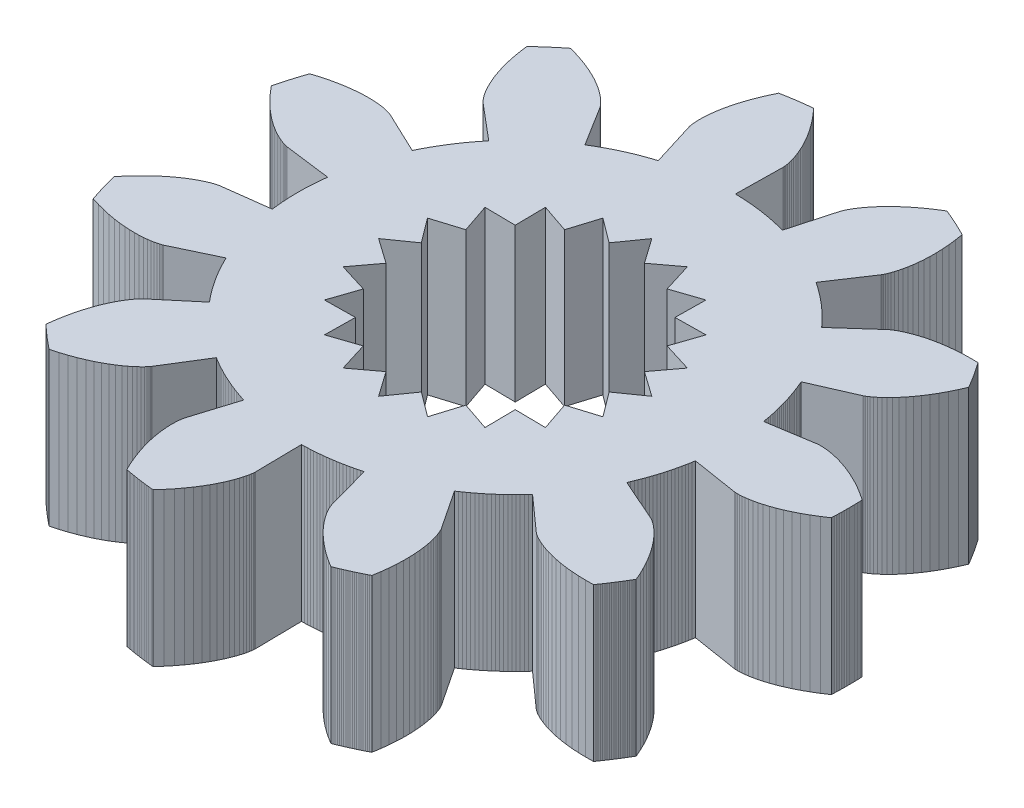
SolidWorks part; units mm, degrees
ref_plane "Front Plane" through (0, 0, 0) normal (0, 0, 1) x (1, 0, 0)
ref_plane "Top Plane" through (0, 0, 0) normal (0, 1, 0) x (1, 0, 0)
ref_plane "Right Plane" through (0, 0, 0) normal (1, 0, 0) x (0, 0, -1)
sketch "Sketch2" plane through (0, 0, 0) normal (0, 1, 0) x (1, 0, 0)
  line L0 (4.1973, -0.6675) -> (5.1042, -0.8117)
  line L1 (5.1042, -0.8117) -> (5.1083, -0.8122)
  line L2 (5.1083, -0.8122) -> (5.1207, -0.8134)
  line L3 (5.1207, -0.8134) -> (5.1415, -0.8146)
  line L4 (5.1415, -0.8146) -> (5.1707, -0.8151)
  line L5 (5.1707, -0.8151) -> (5.2081, -0.8142)
  line L6 (5.2081, -0.8142) -> (5.2538, -0.8113)
  line L7 (5.2538, -0.8113) -> (5.3077, -0.8057)
  line L8 (5.3077, -0.8057) -> (5.3695, -0.7967)
  line L9 (5.3695, -0.7967) -> (5.4391, -0.7838)
  line L10 (5.4391, -0.7838) -> (5.5162, -0.7662)
  line L11 (5.5162, -0.7662) -> (5.6006, -0.7434)
  line L12 (5.6006, -0.7434) -> (5.692, -0.7147)
  line L13 (5.692, -0.7147) -> (5.79, -0.6795)
  line L14 (5.79, -0.6795) -> (5.8942, -0.6374)
  line L15 (5.8942, -0.6374) -> (6.0042, -0.5876)
  line L16 (6.0042, -0.5876) -> (6.1196, -0.5298)
  line L17 (6.1196, -0.5298) -> (6.2399, -0.4633)
  line L18 (6.2399, -0.4633) -> (6.3645, -0.3878)
  line L19 (6.3645, -0.3878) -> (6.4929, -0.3027)
  line L20 (6.4929, -0.3027) -> (6.4944, -0.2708)
  line L21 (6.4944, -0.2708) -> (6.4956, -0.239)
  line L22 (6.4956, -0.239) -> (6.4967, -0.2071)
  line L23 (6.4967, -0.2071) -> (6.4976, -0.1753)
  line L24 (6.4976, -0.1753) -> (6.4984, -0.1434)
  line L25 (6.4984, -0.1434) -> (6.499, -0.1115)
  line L26 (6.499, -0.1115) -> (6.4995, -0.0797)
  line L27 (6.4995, -0.0797) -> (6.4998, -0.0478)
  line L28 (6.4998, -0.0478) -> (6.5, -0.0159)
  line L29 (6.5, -0.0159) -> (6.5, 0.0159)
  line L30 (6.5, 0.0159) -> (6.4998, 0.0478)
  line L31 (6.4998, 0.0478) -> (6.4995, 0.0797)
  line L32 (6.4995, 0.0797) -> (6.499, 0.1115)
  line L33 (6.499, 0.1115) -> (6.4984, 0.1434)
  line L34 (6.4984, 0.1434) -> (6.4976, 0.1753)
  line L35 (6.4976, 0.1753) -> (6.4967, 0.2071)
  line L36 (6.4967, 0.2071) -> (6.4956, 0.239)
  line L37 (6.4956, 0.239) -> (6.4944, 0.2708)
  line L38 (6.4944, 0.2708) -> (6.4929, 0.3027)
  line L39 (6.4929, 0.3027) -> (6.3645, 0.3878)
  line L40 (6.3645, 0.3878) -> (6.2399, 0.4633)
  line L41 (6.2399, 0.4633) -> (6.1196, 0.5298)
  line L42 (6.1196, 0.5298) -> (6.0042, 0.5876)
  line L43 (6.0042, 0.5876) -> (5.8942, 0.6374)
  line L44 (5.8942, 0.6374) -> (5.79, 0.6795)
  line L45 (5.79, 0.6795) -> (5.692, 0.7147)
  line L46 (5.692, 0.7147) -> (5.6006, 0.7434)
  line L47 (5.6006, 0.7434) -> (5.5162, 0.7662)
  line L48 (5.5162, 0.7662) -> (5.4391, 0.7838)
  line L49 (5.4391, 0.7838) -> (5.3695, 0.7967)
  line L50 (5.3695, 0.7967) -> (5.3077, 0.8057)
  line L51 (5.3077, 0.8057) -> (5.2538, 0.8113)
  line L52 (5.2538, 0.8113) -> (5.2081, 0.8142)
  line L53 (5.2081, 0.8142) -> (5.1707, 0.8151)
  line L54 (5.1707, 0.8151) -> (5.1415, 0.8146)
  line L55 (5.1415, 0.8146) -> (5.1207, 0.8134)
  line L56 (5.1207, 0.8134) -> (5.1083, 0.8122)
  line L57 (5.1083, 0.8122) -> (5.1042, 0.8117)
  line L58 (5.1042, 0.8117) -> (4.1973, 0.6675)
  line L59 (4.1973, 0.6675) -> (4.1879, 0.7239)
  line L60 (4.1879, 0.7239) -> (4.1778, 0.7802)
  line L61 (4.1778, 0.7802) -> (4.1669, 0.8364)
  line L62 (4.1669, 0.8364) -> (4.1552, 0.8924)
  line L63 (4.1552, 0.8924) -> (4.1429, 0.9483)
  line L64 (4.1429, 0.9483) -> (4.1297, 1.004)
  line L65 (4.1297, 1.004) -> (4.1158, 1.0595)
  line L66 (4.1158, 1.0595) -> (4.1012, 1.1148)
  line L67 (4.1012, 1.1148) -> (4.0858, 1.1699)
  line L68 (4.0858, 1.1699) -> (4.0697, 1.2248)
  line L69 (4.0697, 1.2248) -> (4.0528, 1.2795)
  line L70 (4.0528, 1.2795) -> (4.0352, 1.3339)
  line L71 (4.0352, 1.3339) -> (4.0169, 1.3881)
  line L72 (4.0169, 1.3881) -> (3.9979, 1.4421)
  line L73 (3.9979, 1.4421) -> (3.9781, 1.4957)
  line L74 (3.9781, 1.4957) -> (3.9576, 1.5492)
  line L75 (3.9576, 1.5492) -> (3.9364, 1.6023)
  line L76 (3.9364, 1.6023) -> (3.9145, 1.6552)
  line L77 (3.9145, 1.6552) -> (3.8918, 1.7077)
  line L78 (3.8918, 1.7077) -> (4.7327, 2.0767)
  line L79 (4.7327, 2.0767) -> (4.7365, 2.0785)
  line L80 (4.7365, 2.0785) -> (4.7476, 2.0842)
  line L81 (4.7476, 2.0842) -> (4.7657, 2.0944)
  line L82 (4.7657, 2.0944) -> (4.7905, 2.1098)
  line L83 (4.7905, 2.1098) -> (4.8215, 2.1308)
  line L84 (4.8215, 2.1308) -> (4.8584, 2.158)
  line L85 (4.8584, 2.158) -> (4.9007, 2.1918)
  line L86 (4.9007, 2.1918) -> (4.9478, 2.2327)
  line L87 (4.9478, 2.2327) -> (4.9994, 2.2813)
  line L88 (4.9994, 2.2813) -> (5.0548, 2.3377)
  line L89 (5.0548, 2.3377) -> (5.1134, 2.4026)
  line L90 (5.1134, 2.4026) -> (5.1748, 2.4761)
  line L91 (5.1748, 2.4761) -> (5.2382, 2.5586)
  line L92 (5.2382, 2.5586) -> (5.3031, 2.6505)
  line L93 (5.3031, 2.6505) -> (5.3688, 2.7518)
  line L94 (5.3688, 2.7518) -> (5.4346, 2.8628)
  line L95 (5.4346, 2.8628) -> (5.4998, 2.9838)
  line L96 (5.4998, 2.9838) -> (5.5638, 3.1147)
  line L97 (5.5638, 3.1147) -> (5.6259, 3.2557)
  line L98 (5.6259, 3.2557) -> (5.6098, 3.2833)
  line L99 (5.6098, 3.2833) -> (5.5937, 3.3107)
  line L100 (5.5937, 3.3107) -> (5.5774, 3.3381)
  line L101 (5.5774, 3.3381) -> (5.5609, 3.3654)
  line L102 (5.5609, 3.3654) -> (5.5444, 3.3927)
  line L103 (5.5444, 3.3927) -> (5.5276, 3.4198)
  line L104 (5.5276, 3.4198) -> (5.5108, 3.4469)
  line L105 (5.5108, 3.4469) -> (5.4938, 3.4739)
  line L106 (5.4938, 3.4739) -> (5.4767, 3.5007)
  line L107 (5.4767, 3.5007) -> (5.4595, 3.5276)
  line L108 (5.4595, 3.5276) -> (5.4422, 3.5543)
  line L109 (5.4422, 3.5543) -> (5.4247, 3.5809)
  line L110 (5.4247, 3.5809) -> (5.407, 3.6075)
  line L111 (5.407, 3.6075) -> (5.3893, 3.634)
  line L112 (5.3893, 3.634) -> (5.3714, 3.6603)
  line L113 (5.3714, 3.6603) -> (5.3534, 3.6866)
  line L114 (5.3534, 3.6866) -> (5.3352, 3.7128)
  line L115 (5.3352, 3.7128) -> (5.317, 3.739)
  line L116 (5.317, 3.739) -> (5.2986, 3.765)
  line L117 (5.2986, 3.765) -> (5.1445, 3.7671)
  line L118 (5.1445, 3.7671) -> (4.9988, 3.7633)
  line L119 (4.9988, 3.7633) -> (4.8617, 3.7542)
  line L120 (4.8617, 3.7542) -> (4.7334, 3.7405)
  line L121 (4.7334, 3.7405) -> (4.6139, 3.7228)
  line L122 (4.6139, 3.7228) -> (4.5035, 3.702)
  line L123 (4.5035, 3.702) -> (4.402, 3.6785)
  line L124 (4.402, 3.6785) -> (4.3097, 3.6533)
  line L125 (4.3097, 3.6533) -> (4.2263, 3.6268)
  line L126 (4.2263, 3.6268) -> (4.1519, 3.5999)
  line L127 (4.1519, 3.5999) -> (4.0864, 3.5732)
  line L128 (4.0864, 3.5732) -> (4.0295, 3.5473)
  line L129 (4.0295, 3.5473) -> (3.9812, 3.5229)
  line L130 (3.9812, 3.5229) -> (3.9412, 3.5007)
  line L131 (3.9412, 3.5007) -> (3.9092, 3.4811)
  line L132 (3.9092, 3.4811) -> (3.8849, 3.465)
  line L133 (3.8849, 3.465) -> (3.8681, 3.4528)
  line L134 (3.8681, 3.4528) -> (3.8583, 3.445)
  line L135 (3.8583, 3.445) -> (3.8551, 3.4424)
  line L136 (3.8551, 3.4424) -> (3.1701, 2.8307)
  line L137 (3.1701, 2.8307) -> (3.1317, 2.8731)
  line L138 (3.1317, 2.8731) -> (3.0927, 2.915)
  line L139 (3.0927, 2.915) -> (3.0532, 2.9564)
  line L140 (3.0532, 2.9564) -> (3.0131, 2.9972)
  line L141 (3.0131, 2.9972) -> (2.9725, 3.0375)
  line L142 (2.9725, 3.0375) -> (2.9314, 3.0773)
  line L143 (2.9314, 3.0773) -> (2.8897, 3.1165)
  line L144 (2.8897, 3.1165) -> (2.8474, 3.1551)
  line L145 (2.8474, 3.1551) -> (2.8047, 3.1931)
  line L146 (2.8047, 3.1931) -> (2.7615, 3.2306)
  line L147 (2.7615, 3.2306) -> (2.7177, 3.2675)
  line L148 (2.7177, 3.2675) -> (2.6735, 3.3038)
  line L149 (2.6735, 3.3038) -> (2.6288, 3.3395)
  line L150 (2.6288, 3.3395) -> (2.5836, 3.3745)
  line L151 (2.5836, 3.3745) -> (2.5379, 3.409)
  line L152 (2.5379, 3.409) -> (2.4918, 3.4429)
  line L153 (2.4918, 3.4429) -> (2.4452, 3.4761)
  line L154 (2.4452, 3.4761) -> (2.3982, 3.5087)
  line L155 (2.3982, 3.5087) -> (2.3508, 3.5407)
  line L156 (2.3508, 3.5407) -> (2.8587, 4.3057)
  line L157 (2.8587, 4.3057) -> (2.8609, 4.3093)
  line L158 (2.8609, 4.3093) -> (2.8671, 4.3201)
  line L159 (2.8671, 4.3201) -> (2.8768, 4.3385)
  line L160 (2.8768, 4.3385) -> (2.8894, 4.3648)
  line L161 (2.8894, 4.3648) -> (2.9041, 4.3993)
  line L162 (2.9041, 4.3993) -> (2.9205, 4.4421)
  line L163 (2.9205, 4.4421) -> (2.9377, 4.4934)
  line L164 (2.9377, 4.4934) -> (2.9553, 4.5533)
  line L165 (2.9553, 4.5533) -> (2.9724, 4.622)
  line L166 (2.9724, 4.622) -> (2.9885, 4.6994)
  line L167 (2.9885, 4.6994) -> (3.0028, 4.7857)
  line L168 (3.0028, 4.7857) -> (3.0146, 4.8807)
  line L169 (3.0146, 4.8807) -> (3.0234, 4.9845)
  line L170 (3.0234, 4.9845) -> (3.0283, 5.0968)
  line L171 (3.0283, 5.0968) -> (3.0288, 5.2175)
  line L172 (3.0288, 5.2175) -> (3.0241, 5.3465)
  line L173 (3.0241, 5.3465) -> (3.0136, 5.4835)
  line L174 (3.0136, 5.4835) -> (2.9966, 5.6283)
  line L175 (2.9966, 5.6283) -> (2.9726, 5.7805)
  line L176 (2.9726, 5.7805) -> (2.9442, 5.795)
  line L177 (2.9442, 5.795) -> (2.9158, 5.8093)
  line L178 (2.9158, 5.8093) -> (2.8872, 5.8236)
  line L179 (2.8872, 5.8236) -> (2.8586, 5.8376)
  line L180 (2.8586, 5.8376) -> (2.83, 5.8516)
  line L181 (2.83, 5.8516) -> (2.8013, 5.8654)
  line L182 (2.8013, 5.8654) -> (2.7725, 5.8791)
  line L183 (2.7725, 5.8791) -> (2.7436, 5.8926)
  line L184 (2.7436, 5.8926) -> (2.7147, 5.906)
  line L185 (2.7147, 5.906) -> (2.6857, 5.9192)
  line L186 (2.6857, 5.9192) -> (2.6566, 5.9323)
  line L187 (2.6566, 5.9323) -> (2.6275, 5.9453)
  line L188 (2.6275, 5.9453) -> (2.5983, 5.9581)
  line L189 (2.5983, 5.9581) -> (2.5691, 5.9707)
  line L190 (2.5691, 5.9707) -> (2.5398, 5.9833)
  line L191 (2.5398, 5.9833) -> (2.5104, 5.9957)
  line L192 (2.5104, 5.9957) -> (2.481, 6.0079)
  line L193 (2.481, 6.0079) -> (2.4515, 6.02)
  line L194 (2.4515, 6.02) -> (2.4219, 6.0319)
  line L195 (2.4219, 6.0319) -> (2.2912, 5.9504)
  line L196 (2.2912, 5.9504) -> (2.1707, 5.8685)
  line L197 (2.1707, 5.8685) -> (2.0603, 5.7867)
  line L198 (2.0603, 5.7867) -> (1.9597, 5.7057)
  line L199 (1.9597, 5.7057) -> (1.8688, 5.6263)
  line L200 (1.8688, 5.6263) -> (1.7871, 5.549)
  line L201 (1.7871, 5.549) -> (1.7145, 5.4745)
  line L202 (1.7145, 5.4745) -> (1.6504, 5.4033)
  line L203 (1.6504, 5.4033) -> (1.5946, 5.336)
  line L204 (1.5946, 5.336) -> (1.5465, 5.2731)
  line L205 (1.5465, 5.2731) -> (1.5059, 5.2152)
  line L206 (1.5059, 5.2152) -> (1.472, 5.1627)
  line L207 (1.472, 5.1627) -> (1.4446, 5.1161)
  line L208 (1.4446, 5.1161) -> (1.4229, 5.0757)
  line L209 (1.4229, 5.0757) -> (1.4066, 5.042)
  line L210 (1.4066, 5.042) -> (1.3949, 5.0153)
  line L211 (1.3949, 5.0153) -> (1.3873, 4.9959)
  line L212 (1.3873, 4.9959) -> (1.3832, 4.9841)
  line L213 (1.3832, 4.9841) -> (1.382, 4.9801)
  line L214 (1.382, 4.9801) -> (1.1365, 4.0952)
  line L215 (1.1365, 4.0952) -> (1.0812, 4.1102)
  line L216 (1.0812, 4.1102) -> (1.0258, 4.1243)
  line L217 (1.0258, 4.1243) -> (0.9702, 4.1378)
  line L218 (0.9702, 4.1378) -> (0.9144, 4.1505)
  line L219 (0.9144, 4.1505) -> (0.8584, 4.1624)
  line L220 (0.8584, 4.1624) -> (0.8023, 4.1736)
  line L221 (0.8023, 4.1736) -> (0.7461, 4.184)
  line L222 (0.7461, 4.184) -> (0.6897, 4.1937)
  line L223 (0.6897, 4.1937) -> (0.6331, 4.2026)
  line L224 (0.6331, 4.2026) -> (0.5765, 4.2107)
  line L225 (0.5765, 4.2107) -> (0.5198, 4.2181)
  line L226 (0.5198, 4.2181) -> (0.4629, 4.2247)
  line L227 (0.4629, 4.2247) -> (0.406, 4.2306)
  line L228 (0.406, 4.2306) -> (0.349, 4.2356)
  line L229 (0.349, 4.2356) -> (0.292, 4.24)
  line L230 (0.292, 4.24) -> (0.2349, 4.2435)
  line L231 (0.2349, 4.2435) -> (0.1777, 4.2463)
  line L232 (0.1777, 4.2463) -> (0.1205, 4.2483)
  line L233 (0.1205, 4.2483) -> (0.0633, 4.2495)
  line L234 (0.0633, 4.2495) -> (0.077, 5.1677)
  line L235 (0.077, 5.1677) -> (0.077, 5.1719)
  line L236 (0.077, 5.1719) -> (0.0764, 5.1844)
  line L237 (0.0764, 5.1844) -> (0.0746, 5.2051)
  line L238 (0.0746, 5.2051) -> (0.0709, 5.234)
  line L239 (0.0709, 5.234) -> (0.0647, 5.271)
  line L240 (0.0647, 5.271) -> (0.0553, 5.3158)
  line L241 (0.0553, 5.3158) -> (0.0421, 5.3683)
  line L242 (0.0421, 5.3683) -> (0.0244, 5.4282)
  line L243 (0.0244, 5.4282) -> (0.0017, 5.4953)
  line L244 (0.0017, 5.4953) -> (-0.0267, 5.5691)
  line L245 (-0.0267, 5.5691) -> (-0.0613, 5.6494)
  line L246 (-0.0613, 5.6494) -> (-0.1027, 5.7358)
  line L247 (-0.1027, 5.7358) -> (-0.1514, 5.8278)
  line L248 (-0.1514, 5.8278) -> (-0.208, 5.9249)
  line L249 (-0.208, 5.9249) -> (-0.2729, 6.0267)
  line L250 (-0.2729, 6.0267) -> (-0.3465, 6.1327)
  line L251 (-0.3465, 6.1327) -> (-0.4294, 6.2423)
  line L252 (-0.4294, 6.2423) -> (-0.522, 6.3549)
  line L253 (-0.522, 6.3549) -> (-0.6245, 6.4699)
  line L254 (-0.6245, 6.4699) -> (-0.6562, 6.4668)
  line L255 (-0.6562, 6.4668) -> (-0.6879, 6.4635)
  line L256 (-0.6879, 6.4635) -> (-0.7196, 6.46)
  line L257 (-0.7196, 6.46) -> (-0.7512, 6.4564)
  line L258 (-0.7512, 6.4564) -> (-0.7829, 6.4527)
  line L259 (-0.7829, 6.4527) -> (-0.8145, 6.4488)
  line L260 (-0.8145, 6.4488) -> (-0.8461, 6.4447)
  line L261 (-0.8461, 6.4447) -> (-0.8777, 6.4405)
  line L262 (-0.8777, 6.4405) -> (-0.9093, 6.4361)
  line L263 (-0.9093, 6.4361) -> (-0.9408, 6.4316)
  line L264 (-0.9408, 6.4316) -> (-0.9723, 6.4269)
  line L265 (-0.9723, 6.4269) -> (-1.0038, 6.422)
  line L266 (-1.0038, 6.422) -> (-1.0353, 6.417)
  line L267 (-1.0353, 6.417) -> (-1.0668, 6.4119)
  line L268 (-1.0668, 6.4119) -> (-1.0982, 6.4066)
  line L269 (-1.0982, 6.4066) -> (-1.1296, 6.4011)
  line L270 (-1.1296, 6.4011) -> (-1.161, 6.3955)
  line L271 (-1.161, 6.3955) -> (-1.1923, 6.3897)
  line L272 (-1.1923, 6.3897) -> (-1.2236, 6.3838)
  line L273 (-1.2236, 6.3838) -> (-1.2896, 6.2445)
  line L274 (-1.2896, 6.2445) -> (-1.3466, 6.1104)
  line L275 (-1.3466, 6.1104) -> (-1.3953, 5.9819)
  line L276 (-1.3953, 5.9819) -> (-1.4361, 5.8595)
  line L277 (-1.4361, 5.8595) -> (-1.4697, 5.7435)
  line L278 (-1.4697, 5.7435) -> (-1.4966, 5.6343)
  line L279 (-1.4966, 5.6343) -> (-1.5175, 5.5324)
  line L280 (-1.5175, 5.5324) -> (-1.5328, 5.4378)
  line L281 (-1.5328, 5.4378) -> (-1.5434, 5.351)
  line L282 (-1.5434, 5.351) -> (-1.5498, 5.2722)
  line L283 (-1.5498, 5.2722) -> (-1.5528, 5.2015)
  line L284 (-1.5528, 5.2015) -> (-1.5528, 5.139)
  line L285 (-1.5528, 5.139) -> (-1.5507, 5.0849)
  line L286 (-1.5507, 5.0849) -> (-1.5471, 5.0393)
  line L287 (-1.5471, 5.0393) -> (-1.5426, 5.002)
  line L288 (-1.5426, 5.002) -> (-1.538, 4.9733)
  line L289 (-1.538, 4.9733) -> (-1.5339, 4.9529)
  line L290 (-1.5339, 4.9529) -> (-1.531, 4.9407)
  line L291 (-1.531, 4.9407) -> (-1.5298, 4.9367)
  line L292 (-1.5298, 4.9367) -> (-1.258, 4.0595)
  line L293 (-1.258, 4.0595) -> (-1.3125, 4.0422)
  line L294 (-1.3125, 4.0422) -> (-1.3668, 4.0242)
  line L295 (-1.3668, 4.0242) -> (-1.4209, 4.0054)
  line L296 (-1.4209, 4.0054) -> (-1.4747, 3.986)
  line L297 (-1.4747, 3.986) -> (-1.5282, 3.9657)
  line L298 (-1.5282, 3.9657) -> (-1.5815, 3.9448)
  line L299 (-1.5815, 3.9448) -> (-1.6344, 3.9232)
  line L300 (-1.6344, 3.9232) -> (-1.6871, 3.9008)
  line L301 (-1.6871, 3.9008) -> (-1.7395, 3.8777)
  line L302 (-1.7395, 3.8777) -> (-1.7915, 3.854)
  line L303 (-1.7915, 3.854) -> (-1.8432, 3.8295)
  line L304 (-1.8432, 3.8295) -> (-1.8946, 3.8043)
  line L305 (-1.8946, 3.8043) -> (-1.9456, 3.7785)
  line L306 (-1.9456, 3.7785) -> (-1.9963, 3.752)
  line L307 (-1.9963, 3.752) -> (-2.0467, 3.7247)
  line L308 (-2.0467, 3.7247) -> (-2.0966, 3.6968)
  line L309 (-2.0966, 3.6968) -> (-2.1462, 3.6683)
  line L310 (-2.1462, 3.6683) -> (-2.1954, 3.6391)
  line L311 (-2.1954, 3.6391) -> (-2.2442, 3.6092)
  line L312 (-2.2442, 3.6092) -> (-2.7291, 4.389)
  line L313 (-2.7291, 4.389) -> (-2.7314, 4.3925)
  line L314 (-2.7314, 4.3925) -> (-2.7386, 4.4027)
  line L315 (-2.7386, 4.4027) -> (-2.7514, 4.4191)
  line L316 (-2.7514, 4.4191) -> (-2.7701, 4.4415)
  line L317 (-2.7701, 4.4415) -> (-2.7953, 4.4692)
  line L318 (-2.7953, 4.4692) -> (-2.8274, 4.5018)
  line L319 (-2.8274, 4.5018) -> (-2.8669, 4.5389)
  line L320 (-2.8669, 4.5389) -> (-2.9142, 4.5797)
  line L321 (-2.9142, 4.5797) -> (-2.9695, 4.6238)
  line L322 (-2.9695, 4.6238) -> (-3.0333, 4.6706)
  line L323 (-3.0333, 4.6706) -> (-3.1058, 4.7195)
  line L324 (-3.1058, 4.7195) -> (-3.1874, 4.7697)
  line L325 (-3.1874, 4.7697) -> (-3.2781, 4.8208)
  line L326 (-3.2781, 4.8208) -> (-3.3782, 4.8719)
  line L327 (-3.3782, 4.8719) -> (-3.4878, 4.9225)
  line L328 (-3.4878, 4.9225) -> (-3.6071, 4.9718)
  line L329 (-3.6071, 4.9718) -> (-3.7361, 5.0192)
  line L330 (-3.7361, 5.0192) -> (-3.8748, 5.0639)
  line L331 (-3.8748, 5.0639) -> (-4.0232, 5.1053)
  line L332 (-4.0232, 5.1053) -> (-4.0482, 5.0855)
  line L333 (-4.0482, 5.0855) -> (-4.0731, 5.0656)
  line L334 (-4.0731, 5.0656) -> (-4.0979, 5.0455)
  line L335 (-4.0979, 5.0455) -> (-4.1226, 5.0254)
  line L336 (-4.1226, 5.0254) -> (-4.1472, 5.0051)
  line L337 (-4.1472, 5.0051) -> (-4.1717, 4.9847)
  line L338 (-4.1717, 4.9847) -> (-4.1961, 4.9642)
  line L339 (-4.1961, 4.9642) -> (-4.2203, 4.9435)
  line L340 (-4.2203, 4.9435) -> (-4.2445, 4.9228)
  line L341 (-4.2445, 4.9228) -> (-4.2686, 4.9019)
  line L342 (-4.2686, 4.9019) -> (-4.2926, 4.8809)
  line L343 (-4.2926, 4.8809) -> (-4.3165, 4.8598)
  line L344 (-4.3165, 4.8598) -> (-4.3403, 4.8386)
  line L345 (-4.3403, 4.8386) -> (-4.3639, 4.8173)
  line L346 (-4.3639, 4.8173) -> (-4.3875, 4.7958)
  line L347 (-4.3875, 4.7958) -> (-4.411, 4.7742)
  line L348 (-4.411, 4.7742) -> (-4.4343, 4.7526)
  line L349 (-4.4343, 4.7526) -> (-4.4576, 4.7308)
  line L350 (-4.4576, 4.7308) -> (-4.4807, 4.7088)
  line L351 (-4.4807, 4.7088) -> (-4.4609, 4.5561)
  line L352 (-4.4609, 4.5561) -> (-4.4364, 4.4124)
  line L353 (-4.4364, 4.4124) -> (-4.4079, 4.278)
  line L354 (-4.4079, 4.278) -> (-4.376, 4.1529)
  line L355 (-4.376, 4.1529) -> (-4.3416, 4.0372)
  line L356 (-4.3416, 4.0372) -> (-4.3052, 3.9308)
  line L357 (-4.3052, 3.9308) -> (-4.2676, 3.8337)
  line L358 (-4.2676, 3.8337) -> (-4.2294, 3.7459)
  line L359 (-4.2294, 3.7459) -> (-4.1914, 3.6671)
  line L360 (-4.1914, 3.6671) -> (-4.1542, 3.5973)
  line L361 (-4.1542, 3.5973) -> (-4.1184, 3.5363)
  line L362 (-4.1184, 3.5363) -> (-4.0847, 3.4837)
  line L363 (-4.0847, 3.4837) -> (-4.0536, 3.4393)
  line L364 (-4.0536, 3.4393) -> (-4.0259, 3.4029)
  line L365 (-4.0259, 3.4029) -> (-4.002, 3.374)
  line L366 (-4.002, 3.374) -> (-3.9826, 3.3523)
  line L367 (-3.9826, 3.3523) -> (-3.9681, 3.3373)
  line L368 (-3.9681, 3.3373) -> (-3.9591, 3.3287)
  line L369 (-3.9591, 3.3287) -> (-3.956, 3.3259)
  line L370 (-3.956, 3.3259) -> (-3.2531, 2.735)
  line L371 (-3.2531, 2.735) -> (-3.2896, 2.6909)
  line L372 (-3.2896, 2.6909) -> (-3.3255, 2.6464)
  line L373 (-3.3255, 2.6464) -> (-3.3608, 2.6014)
  line L374 (-3.3608, 2.6014) -> (-3.3956, 2.5559)
  line L375 (-3.3956, 2.5559) -> (-3.4297, 2.51)
  line L376 (-3.4297, 2.51) -> (-3.4631, 2.4636)
  line L377 (-3.4631, 2.4636) -> (-3.496, 2.4167)
  line L378 (-3.496, 2.4167) -> (-3.5282, 2.3695)
  line L379 (-3.5282, 2.3695) -> (-3.5598, 2.3217)
  line L380 (-3.5598, 2.3217) -> (-3.5907, 2.2736)
  line L381 (-3.5907, 2.2736) -> (-3.621, 2.2251)
  line L382 (-3.621, 2.2251) -> (-3.6506, 2.1761)
  line L383 (-3.6506, 2.1761) -> (-3.6796, 2.1268)
  line L384 (-3.6796, 2.1268) -> (-3.7079, 2.077)
  line L385 (-3.7079, 2.077) -> (-3.7355, 2.0269)
  line L386 (-3.7355, 2.0269) -> (-3.7625, 1.9765)
  line L387 (-3.7625, 1.9765) -> (-3.7887, 1.9256)
  line L388 (-3.7887, 1.9256) -> (-3.8143, 1.8745)
  line L389 (-3.8143, 1.8745) -> (-3.8392, 1.8229)
  line L390 (-3.8392, 1.8229) -> (-4.6687, 2.2168)
  line L391 (-4.6687, 2.2168) -> (-4.6725, 2.2185)
  line L392 (-4.6725, 2.2185) -> (-4.6841, 2.2231)
  line L393 (-4.6841, 2.2231) -> (-4.7038, 2.2301)
  line L394 (-4.7038, 2.2301) -> (-4.7316, 2.2388)
  line L395 (-4.7316, 2.2388) -> (-4.7678, 2.2485)
  line L396 (-4.7678, 2.2485) -> (-4.8125, 2.2586)
  line L397 (-4.8125, 2.2586) -> (-4.8657, 2.2684)
  line L398 (-4.8657, 2.2684) -> (-4.9275, 2.2772)
  line L399 (-4.9275, 2.2772) -> (-4.998, 2.2844)
  line L400 (-4.998, 2.2844) -> (-5.0769, 2.2892)
  line L401 (-5.0769, 2.2892) -> (-5.1643, 2.2911)
  line L402 (-5.1643, 2.2911) -> (-5.2601, 2.2893)
  line L403 (-5.2601, 2.2893) -> (-5.364, 2.2832)
  line L404 (-5.364, 2.2832) -> (-5.4759, 2.2721)
  line L405 (-5.4759, 2.2721) -> (-5.5955, 2.2554)
  line L406 (-5.5955, 2.2554) -> (-5.7225, 2.2324)
  line L407 (-5.7225, 2.2324) -> (-5.8566, 2.2025)
  line L408 (-5.8566, 2.2025) -> (-5.9975, 2.1651)
  line L409 (-5.9975, 2.1651) -> (-6.1447, 2.1197)
  line L410 (-6.1447, 2.1197) -> (-6.155, 2.0895)
  line L411 (-6.155, 2.0895) -> (-6.1652, 2.0593)
  line L412 (-6.1652, 2.0593) -> (-6.1752, 2.0291)
  line L413 (-6.1752, 2.0291) -> (-6.1851, 1.9988)
  line L414 (-6.1851, 1.9988) -> (-6.1948, 1.9684)
  line L415 (-6.1948, 1.9684) -> (-6.2044, 1.938)
  line L416 (-6.2044, 1.938) -> (-6.2138, 1.9076)
  line L417 (-6.2138, 1.9076) -> (-6.2231, 1.8771)
  line L418 (-6.2231, 1.8771) -> (-6.2322, 1.8465)
  line L419 (-6.2322, 1.8465) -> (-6.2412, 1.816)
  line L420 (-6.2412, 1.816) -> (-6.25, 1.7853)
  line L421 (-6.25, 1.7853) -> (-6.2587, 1.7547)
  line L422 (-6.2587, 1.7547) -> (-6.2672, 1.724)
  line L423 (-6.2672, 1.724) -> (-6.2756, 1.6932)
  line L424 (-6.2756, 1.6932) -> (-6.2838, 1.6624)
  line L425 (-6.2838, 1.6624) -> (-6.2919, 1.6316)
  line L426 (-6.2919, 1.6316) -> (-6.2998, 1.6007)
  line L427 (-6.2998, 1.6007) -> (-6.3076, 1.5698)
  line L428 (-6.3076, 1.5698) -> (-6.3152, 1.5389)
  line L429 (-6.3152, 1.5389) -> (-6.216, 1.421)
  line L430 (-6.216, 1.421) -> (-6.1177, 1.3134)
  line L431 (-6.1177, 1.3134) -> (-6.021, 1.2158)
  line L432 (-6.021, 1.2158) -> (-5.9266, 1.1278)
  line L433 (-5.9266, 1.1278) -> (-5.835, 1.049)
  line L434 (-5.835, 1.049) -> (-5.7469, 0.9792)
  line L435 (-5.7469, 0.9792) -> (-5.6628, 0.9179)
  line L436 (-5.6628, 0.9179) -> (-5.5832, 0.8646)
  line L437 (-5.5832, 0.8646) -> (-5.5086, 0.819)
  line L438 (-5.5086, 0.819) -> (-5.4396, 0.7804)
  line L439 (-5.4396, 0.7804) -> (-5.3764, 0.7483)
  line L440 (-5.3764, 0.7483) -> (-5.3197, 0.7223)
  line L441 (-5.3197, 0.7223) -> (-5.2696, 0.7018)
  line L442 (-5.2696, 0.7018) -> (-5.2265, 0.6861)
  line L443 (-5.2265, 0.6861) -> (-5.1908, 0.6747)
  line L444 (-5.1908, 0.6747) -> (-5.1628, 0.6669)
  line L445 (-5.1628, 0.6669) -> (-5.1425, 0.6622)
  line L446 (-5.1425, 0.6622) -> (-5.1302, 0.6598)
  line L447 (-5.1302, 0.6598) -> (-5.1261, 0.6592)
  line L448 (-5.1261, 0.6592) -> (-4.2153, 0.5421)
  line L449 (-4.2153, 0.5421) -> (-4.2222, 0.4853)
  line L450 (-4.2222, 0.4853) -> (-4.2284, 0.4284)
  line L451 (-4.2284, 0.4284) -> (-4.2337, 0.3714)
  line L452 (-4.2337, 0.3714) -> (-4.2384, 0.3144)
  line L453 (-4.2384, 0.3144) -> (-4.2422, 0.2573)
  line L454 (-4.2422, 0.2573) -> (-4.2453, 0.2002)
  line L455 (-4.2453, 0.2002) -> (-4.2476, 0.143)
  line L456 (-4.2476, 0.143) -> (-4.2491, 0.0858)
  line L457 (-4.2491, 0.0858) -> (-4.2499, 0.0286)
  line L458 (-4.2499, 0.0286) -> (-4.2499, -0.0286)
  line L459 (-4.2499, -0.0286) -> (-4.2491, -0.0858)
  line L460 (-4.2491, -0.0858) -> (-4.2476, -0.143)
  line L461 (-4.2476, -0.143) -> (-4.2453, -0.2002)
  line L462 (-4.2453, -0.2002) -> (-4.2422, -0.2573)
  line L463 (-4.2422, -0.2573) -> (-4.2384, -0.3144)
  line L464 (-4.2384, -0.3144) -> (-4.2337, -0.3714)
  line L465 (-4.2337, -0.3714) -> (-4.2284, -0.4284)
  line L466 (-4.2284, -0.4284) -> (-4.2222, -0.4853)
  line L467 (-4.2222, -0.4853) -> (-4.2153, -0.5421)
  line L468 (-4.2153, -0.5421) -> (-5.1261, -0.6592)
  line L469 (-5.1261, -0.6592) -> (-5.1302, -0.6598)
  line L470 (-5.1302, -0.6598) -> (-5.1425, -0.6622)
  line L471 (-5.1425, -0.6622) -> (-5.1628, -0.6669)
  line L472 (-5.1628, -0.6669) -> (-5.1908, -0.6747)
  line L473 (-5.1908, -0.6747) -> (-5.2265, -0.6861)
  line L474 (-5.2265, -0.6861) -> (-5.2696, -0.7018)
  line L475 (-5.2696, -0.7018) -> (-5.3197, -0.7223)
  line L476 (-5.3197, -0.7223) -> (-5.3764, -0.7483)
  line L477 (-5.3764, -0.7483) -> (-5.4396, -0.7804)
  line L478 (-5.4396, -0.7804) -> (-5.5086, -0.819)
  line L479 (-5.5086, -0.819) -> (-5.5832, -0.8646)
  line L480 (-5.5832, -0.8646) -> (-5.6628, -0.9179)
  line L481 (-5.6628, -0.9179) -> (-5.7469, -0.9792)
  line L482 (-5.7469, -0.9792) -> (-5.835, -1.049)
  line L483 (-5.835, -1.049) -> (-5.9266, -1.1278)
  line L484 (-5.9266, -1.1278) -> (-6.021, -1.2158)
  line L485 (-6.021, -1.2158) -> (-6.1177, -1.3134)
  line L486 (-6.1177, -1.3134) -> (-6.216, -1.421)
  line L487 (-6.216, -1.421) -> (-6.3152, -1.5389)
  line L488 (-6.3152, -1.5389) -> (-6.3076, -1.5698)
  line L489 (-6.3076, -1.5698) -> (-6.2998, -1.6007)
  line L490 (-6.2998, -1.6007) -> (-6.2919, -1.6316)
  line L491 (-6.2919, -1.6316) -> (-6.2838, -1.6624)
  line L492 (-6.2838, -1.6624) -> (-6.2756, -1.6932)
  line L493 (-6.2756, -1.6932) -> (-6.2672, -1.724)
  line L494 (-6.2672, -1.724) -> (-6.2587, -1.7547)
  line L495 (-6.2587, -1.7547) -> (-6.25, -1.7853)
  line L496 (-6.25, -1.7853) -> (-6.2412, -1.816)
  line L497 (-6.2412, -1.816) -> (-6.2322, -1.8465)
  line L498 (-6.2322, -1.8465) -> (-6.2231, -1.8771)
  line L499 (-6.2231, -1.8771) -> (-6.2138, -1.9076)
  line L500 (-6.2138, -1.9076) -> (-6.2044, -1.938)
  line L501 (-6.2044, -1.938) -> (-6.1948, -1.9684)
  line L502 (-6.1948, -1.9684) -> (-6.1851, -1.9988)
  line L503 (-6.1851, -1.9988) -> (-6.1752, -2.0291)
  line L504 (-6.1752, -2.0291) -> (-6.1652, -2.0593)
  line L505 (-6.1652, -2.0593) -> (-6.155, -2.0895)
  line L506 (-6.155, -2.0895) -> (-6.1447, -2.1197)
  line L507 (-6.1447, -2.1197) -> (-5.9975, -2.1651)
  line L508 (-5.9975, -2.1651) -> (-5.8566, -2.2025)
  line L509 (-5.8566, -2.2025) -> (-5.7225, -2.2324)
  line L510 (-5.7225, -2.2324) -> (-5.5955, -2.2554)
  line L511 (-5.5955, -2.2554) -> (-5.4759, -2.2721)
  line L512 (-5.4759, -2.2721) -> (-5.364, -2.2832)
  line L513 (-5.364, -2.2832) -> (-5.2601, -2.2893)
  line L514 (-5.2601, -2.2893) -> (-5.1643, -2.2911)
  line L515 (-5.1643, -2.2911) -> (-5.0769, -2.2892)
  line L516 (-5.0769, -2.2892) -> (-4.998, -2.2844)
  line L517 (-4.998, -2.2844) -> (-4.9275, -2.2772)
  line L518 (-4.9275, -2.2772) -> (-4.8657, -2.2684)
  line L519 (-4.8657, -2.2684) -> (-4.8125, -2.2586)
  line L520 (-4.8125, -2.2586) -> (-4.7678, -2.2485)
  line L521 (-4.7678, -2.2485) -> (-4.7316, -2.2388)
  line L522 (-4.7316, -2.2388) -> (-4.7038, -2.2301)
  line L523 (-4.7038, -2.2301) -> (-4.6841, -2.2231)
  line L524 (-4.6841, -2.2231) -> (-4.6725, -2.2185)
  line L525 (-4.6725, -2.2185) -> (-4.6687, -2.2168)
  line L526 (-4.6687, -2.2168) -> (-3.8392, -1.8229)
  line L527 (-3.8392, -1.8229) -> (-3.8143, -1.8745)
  line L528 (-3.8143, -1.8745) -> (-3.7887, -1.9256)
  line L529 (-3.7887, -1.9256) -> (-3.7625, -1.9765)
  line L530 (-3.7625, -1.9765) -> (-3.7355, -2.0269)
  line L531 (-3.7355, -2.0269) -> (-3.7079, -2.077)
  line L532 (-3.7079, -2.077) -> (-3.6796, -2.1268)
  line L533 (-3.6796, -2.1268) -> (-3.6506, -2.1761)
  line L534 (-3.6506, -2.1761) -> (-3.621, -2.2251)
  line L535 (-3.621, -2.2251) -> (-3.5907, -2.2736)
  line L536 (-3.5907, -2.2736) -> (-3.5598, -2.3217)
  line L537 (-3.5598, -2.3217) -> (-3.5282, -2.3695)
  line L538 (-3.5282, -2.3695) -> (-3.496, -2.4167)
  line L539 (-3.496, -2.4167) -> (-3.4631, -2.4636)
  line L540 (-3.4631, -2.4636) -> (-3.4297, -2.51)
  line L541 (-3.4297, -2.51) -> (-3.3956, -2.5559)
  line L542 (-3.3956, -2.5559) -> (-3.3608, -2.6014)
  line L543 (-3.3608, -2.6014) -> (-3.3255, -2.6464)
  line L544 (-3.3255, -2.6464) -> (-3.2896, -2.6909)
  line L545 (-3.2896, -2.6909) -> (-3.2531, -2.735)
  line L546 (-3.2531, -2.735) -> (-3.956, -3.3259)
  line L547 (-3.956, -3.3259) -> (-3.9591, -3.3287)
  line L548 (-3.9591, -3.3287) -> (-3.9681, -3.3373)
  line L549 (-3.9681, -3.3373) -> (-3.9826, -3.3523)
  line L550 (-3.9826, -3.3523) -> (-4.002, -3.374)
  line L551 (-4.002, -3.374) -> (-4.0259, -3.4029)
  line L552 (-4.0259, -3.4029) -> (-4.0536, -3.4393)
  line L553 (-4.0536, -3.4393) -> (-4.0847, -3.4837)
  line L554 (-4.0847, -3.4837) -> (-4.1184, -3.5363)
  line L555 (-4.1184, -3.5363) -> (-4.1542, -3.5973)
  line L556 (-4.1542, -3.5973) -> (-4.1914, -3.6671)
  line L557 (-4.1914, -3.6671) -> (-4.2294, -3.7459)
  line L558 (-4.2294, -3.7459) -> (-4.2676, -3.8337)
  line L559 (-4.2676, -3.8337) -> (-4.3052, -3.9308)
  line L560 (-4.3052, -3.9308) -> (-4.3416, -4.0372)
  line L561 (-4.3416, -4.0372) -> (-4.376, -4.1529)
  line L562 (-4.376, -4.1529) -> (-4.4079, -4.278)
  line L563 (-4.4079, -4.278) -> (-4.4364, -4.4124)
  line L564 (-4.4364, -4.4124) -> (-4.4609, -4.5561)
  line L565 (-4.4609, -4.5561) -> (-4.4807, -4.7088)
  line L566 (-4.4807, -4.7088) -> (-4.4576, -4.7308)
  line L567 (-4.4576, -4.7308) -> (-4.4343, -4.7526)
  line L568 (-4.4343, -4.7526) -> (-4.411, -4.7742)
  line L569 (-4.411, -4.7742) -> (-4.3875, -4.7958)
  line L570 (-4.3875, -4.7958) -> (-4.3639, -4.8173)
  line L571 (-4.3639, -4.8173) -> (-4.3403, -4.8386)
  line L572 (-4.3403, -4.8386) -> (-4.3165, -4.8598)
  line L573 (-4.3165, -4.8598) -> (-4.2926, -4.8809)
  line L574 (-4.2926, -4.8809) -> (-4.2686, -4.9019)
  line L575 (-4.2686, -4.9019) -> (-4.2445, -4.9228)
  line L576 (-4.2445, -4.9228) -> (-4.2203, -4.9435)
  line L577 (-4.2203, -4.9435) -> (-4.1961, -4.9642)
  line L578 (-4.1961, -4.9642) -> (-4.1717, -4.9847)
  line L579 (-4.1717, -4.9847) -> (-4.1472, -5.0051)
  line L580 (-4.1472, -5.0051) -> (-4.1226, -5.0254)
  line L581 (-4.1226, -5.0254) -> (-4.0979, -5.0455)
  line L582 (-4.0979, -5.0455) -> (-4.0731, -5.0656)
  line L583 (-4.0731, -5.0656) -> (-4.0482, -5.0855)
  line L584 (-4.0482, -5.0855) -> (-4.0232, -5.1053)
  line L585 (-4.0232, -5.1053) -> (-3.8748, -5.0639)
  line L586 (-3.8748, -5.0639) -> (-3.7361, -5.0192)
  line L587 (-3.7361, -5.0192) -> (-3.6071, -4.9718)
  line L588 (-3.6071, -4.9718) -> (-3.4878, -4.9225)
  line L589 (-3.4878, -4.9225) -> (-3.3782, -4.8719)
  line L590 (-3.3782, -4.8719) -> (-3.2781, -4.8208)
  line L591 (-3.2781, -4.8208) -> (-3.1874, -4.7697)
  line L592 (-3.1874, -4.7697) -> (-3.1058, -4.7195)
  line L593 (-3.1058, -4.7195) -> (-3.0333, -4.6706)
  line L594 (-3.0333, -4.6706) -> (-2.9695, -4.6238)
  line L595 (-2.9695, -4.6238) -> (-2.9142, -4.5797)
  line L596 (-2.9142, -4.5797) -> (-2.8669, -4.5389)
  line L597 (-2.8669, -4.5389) -> (-2.8274, -4.5018)
  line L598 (-2.8274, -4.5018) -> (-2.7953, -4.4692)
  line L599 (-2.7953, -4.4692) -> (-2.7701, -4.4415)
  line L600 (-2.7701, -4.4415) -> (-2.7514, -4.4191)
  line L601 (-2.7514, -4.4191) -> (-2.7386, -4.4027)
  line L602 (-2.7386, -4.4027) -> (-2.7314, -4.3925)
  line L603 (-2.7314, -4.3925) -> (-2.7291, -4.389)
  line L604 (-2.7291, -4.389) -> (-2.2442, -3.6092)
  line L605 (-2.2442, -3.6092) -> (-2.1954, -3.6391)
  line L606 (-2.1954, -3.6391) -> (-2.1462, -3.6683)
  line L607 (-2.1462, -3.6683) -> (-2.0966, -3.6968)
  line L608 (-2.0966, -3.6968) -> (-2.0467, -3.7247)
  line L609 (-2.0467, -3.7247) -> (-1.9963, -3.752)
  line L610 (-1.9963, -3.752) -> (-1.9456, -3.7785)
  line L611 (-1.9456, -3.7785) -> (-1.8946, -3.8043)
  line L612 (-1.8946, -3.8043) -> (-1.8432, -3.8295)
  line L613 (-1.8432, -3.8295) -> (-1.7915, -3.854)
  line L614 (-1.7915, -3.854) -> (-1.7395, -3.8777)
  line L615 (-1.7395, -3.8777) -> (-1.6871, -3.9008)
  line L616 (-1.6871, -3.9008) -> (-1.6344, -3.9232)
  line L617 (-1.6344, -3.9232) -> (-1.5815, -3.9448)
  line L618 (-1.5815, -3.9448) -> (-1.5282, -3.9657)
  line L619 (-1.5282, -3.9657) -> (-1.4747, -3.986)
  line L620 (-1.4747, -3.986) -> (-1.4209, -4.0054)
  line L621 (-1.4209, -4.0054) -> (-1.3668, -4.0242)
  line L622 (-1.3668, -4.0242) -> (-1.3125, -4.0422)
  line L623 (-1.3125, -4.0422) -> (-1.258, -4.0595)
  line L624 (-1.258, -4.0595) -> (-1.5298, -4.9367)
  line L625 (-1.5298, -4.9367) -> (-1.531, -4.9407)
  line L626 (-1.531, -4.9407) -> (-1.5339, -4.9529)
  line L627 (-1.5339, -4.9529) -> (-1.538, -4.9733)
  line L628 (-1.538, -4.9733) -> (-1.5426, -5.002)
  line L629 (-1.5426, -5.002) -> (-1.5471, -5.0393)
  line L630 (-1.5471, -5.0393) -> (-1.5507, -5.0849)
  line L631 (-1.5507, -5.0849) -> (-1.5528, -5.139)
  line L632 (-1.5528, -5.139) -> (-1.5528, -5.2015)
  line L633 (-1.5528, -5.2015) -> (-1.5498, -5.2722)
  line L634 (-1.5498, -5.2722) -> (-1.5434, -5.351)
  line L635 (-1.5434, -5.351) -> (-1.5328, -5.4378)
  line L636 (-1.5328, -5.4378) -> (-1.5175, -5.5324)
  line L637 (-1.5175, -5.5324) -> (-1.4966, -5.6343)
  line L638 (-1.4966, -5.6343) -> (-1.4697, -5.7435)
  line L639 (-1.4697, -5.7435) -> (-1.4361, -5.8595)
  line L640 (-1.4361, -5.8595) -> (-1.3953, -5.9819)
  line L641 (-1.3953, -5.9819) -> (-1.3466, -6.1104)
  line L642 (-1.3466, -6.1104) -> (-1.2896, -6.2445)
  line L643 (-1.2896, -6.2445) -> (-1.2236, -6.3838)
  line L644 (-1.2236, -6.3838) -> (-1.1923, -6.3897)
  line L645 (-1.1923, -6.3897) -> (-1.161, -6.3955)
  line L646 (-1.161, -6.3955) -> (-1.1296, -6.4011)
  line L647 (-1.1296, -6.4011) -> (-1.0982, -6.4066)
  line L648 (-1.0982, -6.4066) -> (-1.0668, -6.4119)
  line L649 (-1.0668, -6.4119) -> (-1.0353, -6.417)
  line L650 (-1.0353, -6.417) -> (-1.0038, -6.422)
  line L651 (-1.0038, -6.422) -> (-0.9723, -6.4269)
  line L652 (-0.9723, -6.4269) -> (-0.9408, -6.4316)
  line L653 (-0.9408, -6.4316) -> (-0.9093, -6.4361)
  line L654 (-0.9093, -6.4361) -> (-0.8777, -6.4405)
  line L655 (-0.8777, -6.4405) -> (-0.8461, -6.4447)
  line L656 (-0.8461, -6.4447) -> (-0.8145, -6.4488)
  line L657 (-0.8145, -6.4488) -> (-0.7829, -6.4527)
  line L658 (-0.7829, -6.4527) -> (-0.7512, -6.4564)
  line L659 (-0.7512, -6.4564) -> (-0.7196, -6.46)
  line L660 (-0.7196, -6.46) -> (-0.6879, -6.4635)
  line L661 (-0.6879, -6.4635) -> (-0.6562, -6.4668)
  line L662 (-0.6562, -6.4668) -> (-0.6245, -6.4699)
  line L663 (-0.6245, -6.4699) -> (-0.522, -6.3549)
  line L664 (-0.522, -6.3549) -> (-0.4294, -6.2423)
  line L665 (-0.4294, -6.2423) -> (-0.3465, -6.1327)
  line L666 (-0.3465, -6.1327) -> (-0.2729, -6.0267)
  line L667 (-0.2729, -6.0267) -> (-0.208, -5.9249)
  line L668 (-0.208, -5.9249) -> (-0.1514, -5.8278)
  line L669 (-0.1514, -5.8278) -> (-0.1027, -5.7358)
  line L670 (-0.1027, -5.7358) -> (-0.0613, -5.6494)
  line L671 (-0.0613, -5.6494) -> (-0.0267, -5.5691)
  line L672 (-0.0267, -5.5691) -> (0.0017, -5.4953)
  line L673 (0.0017, -5.4953) -> (0.0244, -5.4282)
  line L674 (0.0244, -5.4282) -> (0.0421, -5.3683)
  line L675 (0.0421, -5.3683) -> (0.0553, -5.3158)
  line L676 (0.0553, -5.3158) -> (0.0647, -5.271)
  line L677 (0.0647, -5.271) -> (0.0709, -5.234)
  line L678 (0.0709, -5.234) -> (0.0746, -5.2051)
  line L679 (0.0746, -5.2051) -> (0.0764, -5.1844)
  line L680 (0.0764, -5.1844) -> (0.077, -5.1719)
  line L681 (0.077, -5.1719) -> (0.077, -5.1677)
  line L682 (0.077, -5.1677) -> (0.0633, -4.2495)
  line L683 (0.0633, -4.2495) -> (0.1205, -4.2483)
  line L684 (0.1205, -4.2483) -> (0.1777, -4.2463)
  line L685 (0.1777, -4.2463) -> (0.2349, -4.2435)
  line L686 (0.2349, -4.2435) -> (0.292, -4.24)
  line L687 (0.292, -4.24) -> (0.349, -4.2356)
  line L688 (0.349, -4.2356) -> (0.406, -4.2306)
  line L689 (0.406, -4.2306) -> (0.4629, -4.2247)
  line L690 (0.4629, -4.2247) -> (0.5198, -4.2181)
  line L691 (0.5198, -4.2181) -> (0.5765, -4.2107)
  line L692 (0.5765, -4.2107) -> (0.6331, -4.2026)
  line L693 (0.6331, -4.2026) -> (0.6897, -4.1937)
  line L694 (0.6897, -4.1937) -> (0.7461, -4.184)
  line L695 (0.7461, -4.184) -> (0.8023, -4.1736)
  line L696 (0.8023, -4.1736) -> (0.8584, -4.1624)
  line L697 (0.8584, -4.1624) -> (0.9144, -4.1505)
  line L698 (0.9144, -4.1505) -> (0.9702, -4.1378)
  line L699 (0.9702, -4.1378) -> (1.0258, -4.1243)
  line L700 (1.0258, -4.1243) -> (1.0812, -4.1102)
  line L701 (1.0812, -4.1102) -> (1.1365, -4.0952)
  line L702 (1.1365, -4.0952) -> (1.382, -4.9801)
  line L703 (1.382, -4.9801) -> (1.3832, -4.9841)
  line L704 (1.3832, -4.9841) -> (1.3873, -4.9959)
  line L705 (1.3873, -4.9959) -> (1.3949, -5.0153)
  line L706 (1.3949, -5.0153) -> (1.4066, -5.042)
  line L707 (1.4066, -5.042) -> (1.4229, -5.0757)
  line L708 (1.4229, -5.0757) -> (1.4446, -5.1161)
  line L709 (1.4446, -5.1161) -> (1.472, -5.1627)
  line L710 (1.472, -5.1627) -> (1.5059, -5.2152)
  line L711 (1.5059, -5.2152) -> (1.5465, -5.2731)
  line L712 (1.5465, -5.2731) -> (1.5946, -5.336)
  line L713 (1.5946, -5.336) -> (1.6504, -5.4033)
  line L714 (1.6504, -5.4033) -> (1.7145, -5.4745)
  line L715 (1.7145, -5.4745) -> (1.7871, -5.549)
  line L716 (1.7871, -5.549) -> (1.8688, -5.6263)
  line L717 (1.8688, -5.6263) -> (1.9597, -5.7057)
  line L718 (1.9597, -5.7057) -> (2.0603, -5.7867)
  line L719 (2.0603, -5.7867) -> (2.1707, -5.8685)
  line L720 (2.1707, -5.8685) -> (2.2912, -5.9504)
  line L721 (2.2912, -5.9504) -> (2.4219, -6.0319)
  line L722 (2.4219, -6.0319) -> (2.4515, -6.02)
  line L723 (2.4515, -6.02) -> (2.481, -6.0079)
  line L724 (2.481, -6.0079) -> (2.5104, -5.9957)
  line L725 (2.5104, -5.9957) -> (2.5398, -5.9833)
  line L726 (2.5398, -5.9833) -> (2.5691, -5.9707)
  line L727 (2.5691, -5.9707) -> (2.5983, -5.9581)
  line L728 (2.5983, -5.9581) -> (2.6275, -5.9453)
  line L729 (2.6275, -5.9453) -> (2.6566, -5.9323)
  line L730 (2.6566, -5.9323) -> (2.6857, -5.9192)
  line L731 (2.6857, -5.9192) -> (2.7147, -5.906)
  line L732 (2.7147, -5.906) -> (2.7436, -5.8926)
  line L733 (2.7436, -5.8926) -> (2.7725, -5.8791)
  line L734 (2.7725, -5.8791) -> (2.8013, -5.8654)
  line L735 (2.8013, -5.8654) -> (2.83, -5.8516)
  line L736 (2.83, -5.8516) -> (2.8586, -5.8376)
  line L737 (2.8586, -5.8376) -> (2.8872, -5.8236)
  line L738 (2.8872, -5.8236) -> (2.9158, -5.8093)
  line L739 (2.9158, -5.8093) -> (2.9442, -5.795)
  line L740 (2.9442, -5.795) -> (2.9726, -5.7805)
  line L741 (2.9726, -5.7805) -> (2.9966, -5.6283)
  line L742 (2.9966, -5.6283) -> (3.0136, -5.4835)
  line L743 (3.0136, -5.4835) -> (3.0241, -5.3465)
  line L744 (3.0241, -5.3465) -> (3.0288, -5.2175)
  line L745 (3.0288, -5.2175) -> (3.0283, -5.0968)
  line L746 (3.0283, -5.0968) -> (3.0234, -4.9845)
  line L747 (3.0234, -4.9845) -> (3.0146, -4.8807)
  line L748 (3.0146, -4.8807) -> (3.0028, -4.7857)
  line L749 (3.0028, -4.7857) -> (2.9885, -4.6994)
  line L750 (2.9885, -4.6994) -> (2.9724, -4.622)
  line L751 (2.9724, -4.622) -> (2.9553, -4.5533)
  line L752 (2.9553, -4.5533) -> (2.9377, -4.4934)
  line L753 (2.9377, -4.4934) -> (2.9205, -4.4421)
  line L754 (2.9205, -4.4421) -> (2.9041, -4.3993)
  line L755 (2.9041, -4.3993) -> (2.8894, -4.3648)
  line L756 (2.8894, -4.3648) -> (2.8768, -4.3385)
  line L757 (2.8768, -4.3385) -> (2.8671, -4.3201)
  line L758 (2.8671, -4.3201) -> (2.8609, -4.3093)
  line L759 (2.8609, -4.3093) -> (2.8587, -4.3057)
  line L760 (2.8587, -4.3057) -> (2.3508, -3.5407)
  line L761 (2.3508, -3.5407) -> (2.3982, -3.5087)
  line L762 (2.3982, -3.5087) -> (2.4452, -3.4761)
  line L763 (2.4452, -3.4761) -> (2.4918, -3.4429)
  line L764 (2.4918, -3.4429) -> (2.5379, -3.409)
  line L765 (2.5379, -3.409) -> (2.5836, -3.3745)
  line L766 (2.5836, -3.3745) -> (2.6288, -3.3395)
  line L767 (2.6288, -3.3395) -> (2.6735, -3.3038)
  line L768 (2.6735, -3.3038) -> (2.7177, -3.2675)
  line L769 (2.7177, -3.2675) -> (2.7615, -3.2306)
  line L770 (2.7615, -3.2306) -> (2.8047, -3.1931)
  line L771 (2.8047, -3.1931) -> (2.8474, -3.1551)
  line L772 (2.8474, -3.1551) -> (2.8897, -3.1165)
  line L773 (2.8897, -3.1165) -> (2.9314, -3.0773)
  line L774 (2.9314, -3.0773) -> (2.9725, -3.0375)
  line L775 (2.9725, -3.0375) -> (3.0131, -2.9972)
  line L776 (3.0131, -2.9972) -> (3.0532, -2.9564)
  line L777 (3.0532, -2.9564) -> (3.0927, -2.915)
  line L778 (3.0927, -2.915) -> (3.1317, -2.8731)
  line L779 (3.1317, -2.8731) -> (3.1701, -2.8307)
  line L780 (3.1701, -2.8307) -> (3.8551, -3.4424)
  line L781 (3.8551, -3.4424) -> (3.8583, -3.445)
  line L782 (3.8583, -3.445) -> (3.8681, -3.4528)
  line L783 (3.8681, -3.4528) -> (3.8849, -3.465)
  line L784 (3.8849, -3.465) -> (3.9092, -3.4811)
  line L785 (3.9092, -3.4811) -> (3.9412, -3.5007)
  line L786 (3.9412, -3.5007) -> (3.9812, -3.5229)
  line L787 (3.9812, -3.5229) -> (4.0295, -3.5473)
  line L788 (4.0295, -3.5473) -> (4.0864, -3.5732)
  line L789 (4.0864, -3.5732) -> (4.1519, -3.5999)
  line L790 (4.1519, -3.5999) -> (4.2263, -3.6268)
  line L791 (4.2263, -3.6268) -> (4.3097, -3.6533)
  line L792 (4.3097, -3.6533) -> (4.402, -3.6785)
  line L793 (4.402, -3.6785) -> (4.5035, -3.702)
  line L794 (4.5035, -3.702) -> (4.6139, -3.7228)
  line L795 (4.6139, -3.7228) -> (4.7334, -3.7405)
  line L796 (4.7334, -3.7405) -> (4.8617, -3.7542)
  line L797 (4.8617, -3.7542) -> (4.9988, -3.7633)
  line L798 (4.9988, -3.7633) -> (5.1445, -3.7671)
  line L799 (5.1445, -3.7671) -> (5.2986, -3.765)
  line L800 (5.2986, -3.765) -> (5.317, -3.739)
  line L801 (5.317, -3.739) -> (5.3352, -3.7128)
  line L802 (5.3352, -3.7128) -> (5.3534, -3.6866)
  line L803 (5.3534, -3.6866) -> (5.3714, -3.6603)
  line L804 (5.3714, -3.6603) -> (5.3893, -3.634)
  line L805 (5.3893, -3.634) -> (5.407, -3.6075)
  line L806 (5.407, -3.6075) -> (5.4247, -3.5809)
  line L807 (5.4247, -3.5809) -> (5.4422, -3.5543)
  line L808 (5.4422, -3.5543) -> (5.4595, -3.5276)
  line L809 (5.4595, -3.5276) -> (5.4767, -3.5007)
  line L810 (5.4767, -3.5007) -> (5.4938, -3.4739)
  line L811 (5.4938, -3.4739) -> (5.5108, -3.4469)
  line L812 (5.5108, -3.4469) -> (5.5276, -3.4198)
  line L813 (5.5276, -3.4198) -> (5.5444, -3.3927)
  line L814 (5.5444, -3.3927) -> (5.5609, -3.3654)
  line L815 (5.5609, -3.3654) -> (5.5774, -3.3381)
  line L816 (5.5774, -3.3381) -> (5.5937, -3.3107)
  line L817 (5.5937, -3.3107) -> (5.6098, -3.2833)
  line L818 (5.6098, -3.2833) -> (5.6259, -3.2557)
  line L819 (5.6259, -3.2557) -> (5.5638, -3.1147)
  line L820 (5.5638, -3.1147) -> (5.4998, -2.9838)
  line L821 (5.4998, -2.9838) -> (5.4346, -2.8628)
  line L822 (5.4346, -2.8628) -> (5.3688, -2.7518)
  line L823 (5.3688, -2.7518) -> (5.3031, -2.6505)
  line L824 (5.3031, -2.6505) -> (5.2382, -2.5586)
  line L825 (5.2382, -2.5586) -> (5.1748, -2.4761)
  line L826 (5.1748, -2.4761) -> (5.1134, -2.4026)
  line L827 (5.1134, -2.4026) -> (5.0548, -2.3377)
  line L828 (5.0548, -2.3377) -> (4.9994, -2.2813)
  line L829 (4.9994, -2.2813) -> (4.9478, -2.2327)
  line L830 (4.9478, -2.2327) -> (4.9007, -2.1918)
  line L831 (4.9007, -2.1918) -> (4.8584, -2.158)
  line L832 (4.8584, -2.158) -> (4.8215, -2.1308)
  line L833 (4.8215, -2.1308) -> (4.7905, -2.1098)
  line L834 (4.7905, -2.1098) -> (4.7657, -2.0944)
  line L835 (4.7657, -2.0944) -> (4.7476, -2.0842)
  line L836 (4.7476, -2.0842) -> (4.7365, -2.0785)
  line L837 (4.7365, -2.0785) -> (4.7327, -2.0767)
  line L838 (4.7327, -2.0767) -> (3.8918, -1.7077)
  line L839 (3.8918, -1.7077) -> (3.9145, -1.6552)
  line L840 (3.9145, -1.6552) -> (3.9364, -1.6023)
  line L841 (3.9364, -1.6023) -> (3.9576, -1.5492)
  line L842 (3.9576, -1.5492) -> (3.9781, -1.4957)
  line L843 (3.9781, -1.4957) -> (3.9979, -1.4421)
  line L844 (3.9979, -1.4421) -> (4.0169, -1.3881)
  line L845 (4.0169, -1.3881) -> (4.0352, -1.3339)
  line L846 (4.0352, -1.3339) -> (4.0528, -1.2795)
  line L847 (4.0528, -1.2795) -> (4.0697, -1.2248)
  line L848 (4.0697, -1.2248) -> (4.0858, -1.1699)
  line L849 (4.0858, -1.1699) -> (4.1012, -1.1148)
  line L850 (4.1012, -1.1148) -> (4.1158, -1.0595)
  line L851 (4.1158, -1.0595) -> (4.1297, -1.004)
  line L852 (4.1297, -1.004) -> (4.1429, -0.9483)
  line L853 (4.1429, -0.9483) -> (4.1552, -0.8924)
  line L854 (4.1552, -0.8924) -> (4.1669, -0.8364)
  line L855 (4.1669, -0.8364) -> (4.1778, -0.7802)
  line L856 (4.1778, -0.7802) -> (4.1879, -0.7239)
  line L857 (4.1879, -0.7239) -> (4.1973, -0.6675)
extrude "Boss-Extrude1" add sketch "Sketch2" along normal blind 3
sketch "Sketch3" plane through (0, 3, 0) normal (0, 1, 0) x (1, 0, 0)
  line L0 (0, 2.675) -> (0, -2.675) construction
  line L1 (-0.346, 2.1848) -> (0, 2.675)
  line L2 (0, 2.675) -> (0.346, 2.1848)
  line L3 (0.346, 2.1848) -> (0.8266, 2.5441)
  line L4 (0.8266, 2.5441) -> (1.0043, 1.971)
  line L5 (1.0043, 1.971) -> (1.5723, 2.1641)
  line L6 (1.5723, 2.1641) -> (1.5642, 1.5642)
  line L7 (1.5642, 1.5642) -> (2.1641, 1.5723)
  line L8 (2.1641, 1.5723) -> (1.971, 1.0043)
  line L9 (1.971, 1.0043) -> (2.5441, 0.8266)
  line L10 (2.5441, 0.8266) -> (2.1848, 0.346)
  line L11 (2.1848, 0.346) -> (2.675, 0)
  line L12 (2.675, 0) -> (2.1848, -0.346)
  line L13 (2.1848, -0.346) -> (2.5441, -0.8266)
  line L14 (2.5441, -0.8266) -> (1.971, -1.0043)
  line L15 (1.971, -1.0043) -> (2.1641, -1.5723)
  line L16 (2.1641, -1.5723) -> (1.5642, -1.5642)
  line L17 (1.5642, -1.5642) -> (1.5723, -2.1641)
  line L18 (1.5723, -2.1641) -> (1.0043, -1.971)
  line L19 (1.0043, -1.971) -> (0.8266, -2.5441)
  line L20 (0.8266, -2.5441) -> (0.346, -2.1848)
  line L21 (0.346, -2.1848) -> (0, -2.675)
  line L22 (0, -2.675) -> (-0.346, -2.1848)
  line L23 (-0.346, -2.1848) -> (-0.8266, -2.5441)
  line L24 (-0.8266, -2.5441) -> (-1.0043, -1.971)
  line L25 (-1.0043, -1.971) -> (-1.5723, -2.1641)
  line L26 (-1.5723, -2.1641) -> (-1.5642, -1.5642)
  line L27 (-1.5642, -1.5642) -> (-2.1641, -1.5723)
  line L28 (-2.1641, -1.5723) -> (-1.971, -1.0043)
  line L29 (-1.971, -1.0043) -> (-2.5441, -0.8266)
  line L30 (-2.5441, -0.8266) -> (-2.1848, -0.346)
  line L31 (-2.1848, -0.346) -> (-2.675, 0)
  line L32 (-2.675, 0) -> (-2.1848, 0.346)
  line L33 (-2.1848, 0.346) -> (-2.5441, 0.8266)
  line L34 (-2.5441, 0.8266) -> (-1.971, 1.0043)
  line L35 (-1.971, 1.0043) -> (-2.1641, 1.5723)
  line L36 (-2.1641, 1.5723) -> (-1.5642, 1.5642)
  line L37 (-1.5642, 1.5642) -> (-1.5723, 2.1641)
  line L38 (-1.5723, 2.1641) -> (-1.0043, 1.971)
  line L39 (-1.0043, 1.971) -> (-0.8266, 2.5441)
  line L40 (-0.8266, 2.5441) -> (-0.346, 2.1848)
  point P1 (0, 0)
  point P63 (0, 0)
  dimension "D1" = 5.35
  dimension "D2" = 0.6
  dimension "D3" = 20
extrude "Cut-Extrude1" cut sketch "Sketch3" against normal through all
